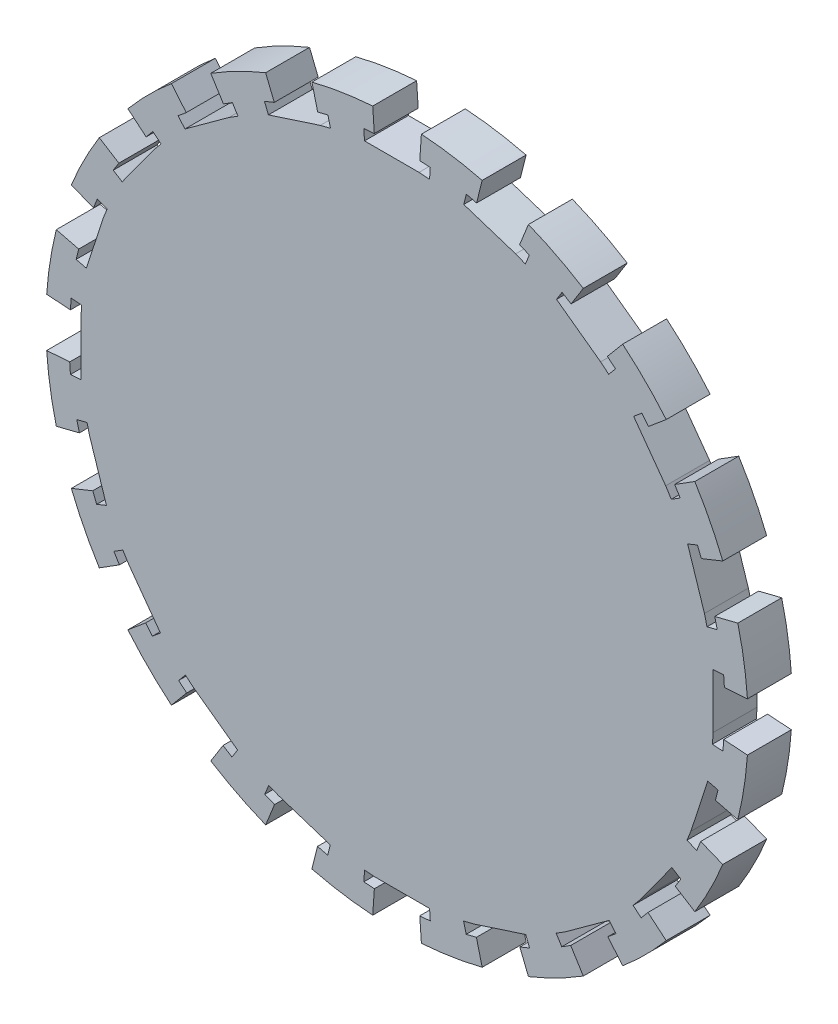
SolidWorks part; units mm, degrees
ref_plane "Front Plane" through (0, 0, 0) normal (0, 0, 1) x (1, 0, 0)
ref_plane "Top Plane" through (0, 0, 0) normal (0, 1, 0) x (1, 0, 0)
ref_plane "Right Plane" through (0, 0, 0) normal (1, 0, 0) x (0, 0, -1)
sketch "Sketch1" plane through (0, 0, 0) normal (0, 0, 1) x (1, 0, 0)
  line L0 (-1.7597, 25.339) -> (-1.5875, 22.86)
  line L1 (-1.5875, 22.86) -> (1.5875, 22.86)
  line L2 (1.5875, 22.86) -> (1.7597, 25.339)
  line L3 (0, 22.86) -> (0, 25.4)
  line L4 (5.5543, 22.2317) -> (8.5739, 21.2506)
  line L5 (8.5739, 21.2506) -> (9.5037, 23.555)
  line L6 (6.1566, 24.6426) -> (5.5543, 22.2317)
  line L7 (12.1525, 19.4272) -> (14.7211, 17.561)
  line L8 (14.7211, 17.561) -> (16.3175, 19.4654)
  line L9 (13.4703, 21.534) -> (12.1525, 19.4272)
  line L10 (17.561, 14.7211) -> (19.4272, 12.1525)
  line L11 (19.4272, 12.1525) -> (21.534, 13.4703)
  line L12 (19.4654, 16.3175) -> (17.561, 14.7211)
  line L13 (21.2506, 8.5739) -> (22.2317, 5.5543)
  line L14 (22.2317, 5.5543) -> (24.6426, 6.1566)
  line L15 (23.555, 9.5037) -> (21.2506, 8.5739)
  line L16 (22.86, 1.5875) -> (22.86, -1.5875)
  line L17 (22.86, -1.5875) -> (25.339, -1.7597)
  line L18 (25.339, 1.7597) -> (22.86, 1.5875)
  line L19 (22.2317, -5.5543) -> (21.2506, -8.5739)
  line L20 (21.2506, -8.5739) -> (23.555, -9.5037)
  line L21 (24.6426, -6.1566) -> (22.2317, -5.5543)
  line L22 (19.4272, -12.1525) -> (17.561, -14.7211)
  line L23 (17.561, -14.7211) -> (19.4654, -16.3175)
  line L24 (21.534, -13.4703) -> (19.4272, -12.1525)
  line L25 (14.7211, -17.561) -> (12.1525, -19.4272)
  line L26 (12.1525, -19.4272) -> (13.4703, -21.534)
  line L27 (16.3175, -19.4654) -> (14.7211, -17.561)
  line L28 (8.5739, -21.2506) -> (5.5543, -22.2317)
  line L29 (5.5543, -22.2317) -> (6.1566, -24.6426)
  line L30 (9.5037, -23.555) -> (8.5739, -21.2506)
  line L31 (1.5875, -22.86) -> (-1.5875, -22.86)
  line L32 (-1.5875, -22.86) -> (-1.7597, -25.339)
  line L33 (1.7597, -25.339) -> (1.5875, -22.86)
  line L34 (-5.5543, -22.2317) -> (-8.5739, -21.2506)
  line L35 (-8.5739, -21.2506) -> (-9.5037, -23.555)
  line L36 (-6.1566, -24.6426) -> (-5.5543, -22.2317)
  line L37 (-12.1525, -19.4272) -> (-14.7211, -17.561)
  line L38 (-14.7211, -17.561) -> (-16.3175, -19.4654)
  line L39 (-13.4703, -21.534) -> (-12.1525, -19.4272)
  line L40 (-17.561, -14.7211) -> (-19.4272, -12.1525)
  line L41 (-19.4272, -12.1525) -> (-21.534, -13.4703)
  line L42 (-19.4654, -16.3175) -> (-17.561, -14.7211)
  line L43 (-21.2506, -8.5739) -> (-22.2317, -5.5543)
  line L44 (-22.2317, -5.5543) -> (-24.6426, -6.1566)
  line L45 (-23.555, -9.5037) -> (-21.2506, -8.5739)
  line L46 (-22.86, -1.5875) -> (-22.86, 1.5875)
  line L47 (-22.86, 1.5875) -> (-25.339, 1.7597)
  line L48 (-25.339, -1.7597) -> (-22.86, -1.5875)
  line L49 (-22.2317, 5.5543) -> (-21.2506, 8.5739)
  line L50 (-21.2506, 8.5739) -> (-23.555, 9.5037)
  line L51 (-24.6426, 6.1566) -> (-22.2317, 5.5543)
  line L52 (-19.4272, 12.1525) -> (-17.561, 14.7211)
  line L53 (-17.561, 14.7211) -> (-19.4654, 16.3175)
  line L54 (-21.534, 13.4703) -> (-19.4272, 12.1525)
  line L55 (-14.7211, 17.561) -> (-12.1525, 19.4272)
  line L56 (-12.1525, 19.4272) -> (-13.4703, 21.534)
  line L57 (-16.3175, 19.4654) -> (-14.7211, 17.561)
  line L58 (-8.5739, 21.2506) -> (-5.5543, 22.2317)
  line L59 (-5.5543, 22.2317) -> (-6.1566, 24.6426)
  line L60 (-9.5037, 23.555) -> (-8.5739, 21.2506)
  line L61 (1.6404, 23.622) -> (2.4024, 23.5691)
  line L62 (2.4024, 23.5691) -> (2.3495, 22.8071)
  line L63 (2.3495, 22.8071) -> (1.5875, 22.86)
  line L64 (-1.644, 23.6731) -> (-2.406, 23.6202)
  line L65 (-2.406, 23.6202) -> (-2.3532, 22.86)
  line L66 (-2.3532, 22.86) -> (-1.5875, 22.86)
  line L67 (5.0108, 23.2076) -> (4.8261, 22.4683)
  line L68 (4.8261, 22.4683) -> (5.5543, 22.2317)
  line L69 (5.7519, 23.0225) -> (5.0108, 23.2076)
  line L70 (8.8597, 21.9589) -> (9.5681, 21.6731)
  line L71 (9.5681, 21.6731) -> (9.2823, 20.9648)
  line L72 (9.2823, 20.9648) -> (8.5739, 21.2506)
  line L73 (11.9371, 20.5233) -> (11.533, 19.8773)
  line L74 (11.533, 19.8773) -> (12.1525, 19.4272)
  line L75 (12.5847, 20.1182) -> (11.9371, 20.5233)
  line L76 (15.2118, 18.1464) -> (15.7972, 17.6557)
  line L77 (15.7972, 17.6557) -> (15.3065, 17.0703)
  line L78 (15.3065, 17.0703) -> (14.7211, 17.561)
  line L79 (17.6949, 15.8301) -> (17.111, 15.3405)
  line L80 (17.111, 15.3405) -> (17.561, 14.7211)
  line L81 (18.1856, 15.2447) -> (17.6949, 15.8301)
  line L82 (20.0748, 12.5575) -> (20.4799, 11.91)
  line L83 (20.4799, 11.91) -> (19.8323, 11.5049)
  line L84 (19.8323, 11.5049) -> (19.4272, 12.1525)
  line L85 (21.7206, 9.5872) -> (21.014, 9.3021)
  line L86 (21.014, 9.3021) -> (21.2506, 8.5739)
  line L87 (22.0064, 8.8789) -> (21.7206, 9.5872)
  line L88 (22.9728, 5.7395) -> (23.1579, 4.9984)
  line L89 (23.1579, 4.9984) -> (22.4169, 4.8133)
  line L90 (22.4169, 4.8133) -> (22.2317, 5.5543)
  line L91 (23.6202, 2.406) -> (22.86, 2.3532)
  line L92 (22.86, 2.3532) -> (22.86, 1.5875)
  line L93 (23.6731, 1.644) -> (23.6202, 2.406)
  line L94 (23.622, -1.6404) -> (23.5691, -2.4024)
  line L95 (23.5691, -2.4024) -> (22.8071, -2.3495)
  line L96 (22.8071, -2.3495) -> (22.86, -1.5875)
  line L97 (23.2076, -5.0108) -> (22.4683, -4.8261)
  line L98 (22.4683, -4.8261) -> (22.2317, -5.5543)
  line L99 (23.0225, -5.7519) -> (23.2076, -5.0108)
  line L100 (21.9589, -8.8597) -> (21.6731, -9.5681)
  line L101 (21.6731, -9.5681) -> (20.9648, -9.2823)
  line L102 (20.9648, -9.2823) -> (21.2506, -8.5739)
  line L103 (20.5233, -11.9371) -> (19.8773, -11.533)
  line L104 (19.8773, -11.533) -> (19.4272, -12.1525)
  line L105 (20.1182, -12.5847) -> (20.5233, -11.9371)
  line L106 (18.1464, -15.2118) -> (17.6557, -15.7972)
  line L107 (17.6557, -15.7972) -> (17.0703, -15.3065)
  line L108 (17.0703, -15.3065) -> (17.561, -14.7211)
  line L109 (15.8301, -17.6949) -> (15.3405, -17.111)
  line L110 (15.3405, -17.111) -> (14.7211, -17.561)
  line L111 (15.2447, -18.1856) -> (15.8301, -17.6949)
  line L112 (12.5575, -20.0748) -> (11.91, -20.4799)
  line L113 (11.91, -20.4799) -> (11.5049, -19.8323)
  line L114 (11.5049, -19.8323) -> (12.1525, -19.4272)
  line L115 (9.5872, -21.7206) -> (9.3021, -21.014)
  line L116 (9.3021, -21.014) -> (8.5739, -21.2506)
  line L117 (8.8789, -22.0064) -> (9.5872, -21.7206)
  line L118 (5.7395, -22.9728) -> (4.9984, -23.1579)
  line L119 (4.9984, -23.1579) -> (4.8133, -22.4169)
  line L120 (4.8133, -22.4169) -> (5.5543, -22.2317)
  line L121 (2.406, -23.6202) -> (2.3532, -22.86)
  line L122 (2.3532, -22.86) -> (1.5875, -22.86)
  line L123 (1.644, -23.6731) -> (2.406, -23.6202)
  line L124 (-1.6404, -23.622) -> (-2.4024, -23.5691)
  line L125 (-2.4024, -23.5691) -> (-2.3495, -22.8071)
  line L126 (-2.3495, -22.8071) -> (-1.5875, -22.86)
  line L127 (-5.0108, -23.2076) -> (-4.8261, -22.4683)
  line L128 (-4.8261, -22.4683) -> (-5.5543, -22.2317)
  line L129 (-5.7519, -23.0225) -> (-5.0108, -23.2076)
  line L130 (-8.8597, -21.9589) -> (-9.5681, -21.6731)
  line L131 (-9.5681, -21.6731) -> (-9.2823, -20.9648)
  line L132 (-9.2823, -20.9648) -> (-8.5739, -21.2506)
  line L133 (-11.9371, -20.5233) -> (-11.533, -19.8773)
  line L134 (-11.533, -19.8773) -> (-12.1525, -19.4272)
  line L135 (-12.5847, -20.1182) -> (-11.9371, -20.5233)
  line L136 (-15.2118, -18.1464) -> (-15.7972, -17.6557)
  line L137 (-15.7972, -17.6557) -> (-15.3065, -17.0703)
  line L138 (-15.3065, -17.0703) -> (-14.7211, -17.561)
  line L139 (-17.6949, -15.8301) -> (-17.111, -15.3405)
  line L140 (-17.111, -15.3405) -> (-17.561, -14.7211)
  line L141 (-18.1856, -15.2447) -> (-17.6949, -15.8301)
  line L142 (-20.0748, -12.5575) -> (-20.4799, -11.91)
  line L143 (-20.4799, -11.91) -> (-19.8323, -11.5049)
  line L144 (-19.8323, -11.5049) -> (-19.4272, -12.1525)
  line L145 (-21.7206, -9.5872) -> (-21.014, -9.3021)
  line L146 (-21.014, -9.3021) -> (-21.2506, -8.5739)
  line L147 (-22.0064, -8.8789) -> (-21.7206, -9.5872)
  line L148 (-22.9728, -5.7395) -> (-23.1579, -4.9984)
  line L149 (-23.1579, -4.9984) -> (-22.4169, -4.8133)
  line L150 (-22.4169, -4.8133) -> (-22.2317, -5.5543)
  line L151 (-23.6202, -2.406) -> (-22.86, -2.3532)
  line L152 (-22.86, -2.3532) -> (-22.86, -1.5875)
  line L153 (-23.6731, -1.644) -> (-23.6202, -2.406)
  line L154 (-23.622, 1.6404) -> (-23.5691, 2.4024)
  line L155 (-23.5691, 2.4024) -> (-22.8071, 2.3495)
  line L156 (-22.8071, 2.3495) -> (-22.86, 1.5875)
  line L157 (-23.2076, 5.0108) -> (-22.4683, 4.8261)
  line L158 (-22.4683, 4.8261) -> (-22.2317, 5.5543)
  line L159 (-23.0225, 5.7519) -> (-23.2076, 5.0108)
  line L160 (-21.9589, 8.8597) -> (-21.6731, 9.5681)
  line L161 (-21.6731, 9.5681) -> (-20.9648, 9.2823)
  line L162 (-20.9648, 9.2823) -> (-21.2506, 8.5739)
  line L163 (-20.5233, 11.9371) -> (-19.8773, 11.533)
  line L164 (-19.8773, 11.533) -> (-19.4272, 12.1525)
  line L165 (-20.1182, 12.5847) -> (-20.5233, 11.9371)
  line L166 (-18.1464, 15.2118) -> (-17.6557, 15.7972)
  line L167 (-17.6557, 15.7972) -> (-17.0703, 15.3065)
  line L168 (-17.0703, 15.3065) -> (-17.561, 14.7211)
  line L169 (-15.8301, 17.6949) -> (-15.3405, 17.111)
  line L170 (-15.3405, 17.111) -> (-14.7211, 17.561)
  line L171 (-15.2447, 18.1856) -> (-15.8301, 17.6949)
  line L172 (-12.5575, 20.0748) -> (-11.91, 20.4799)
  line L173 (-11.91, 20.4799) -> (-11.5049, 19.8323)
  line L174 (-11.5049, 19.8323) -> (-12.1525, 19.4272)
  line L175 (-9.5872, 21.7206) -> (-9.3021, 21.014)
  line L176 (-9.3021, 21.014) -> (-8.5739, 21.2506)
  line L177 (-8.8789, 22.0064) -> (-9.5872, 21.7206)
  line L178 (-5.7395, 22.9728) -> (-4.9984, 23.1579)
  line L179 (-4.9984, 23.1579) -> (-4.8133, 22.4169)
  line L180 (-4.8133, 22.4169) -> (-5.5543, 22.2317)
  arc A0 (-9.5037, 23.555) -> (-13.4703, 21.534) centre (0, 0) ccw
  arc A1 (-16.3175, 19.4654) -> (-19.4654, 16.3175) centre (0, 0) ccw
  arc A2 (-21.534, 13.4703) -> (-23.555, 9.5037) centre (0, 0) ccw
  arc A3 (-24.6426, 6.1566) -> (-25.339, 1.7597) centre (0, 0) ccw
  arc A4 (-25.339, -1.7597) -> (-24.6426, -6.1566) centre (0, 0) ccw
  arc A5 (-23.555, -9.5037) -> (-21.534, -13.4703) centre (0, 0) ccw
  arc A6 (-1.7597, 25.339) -> (-6.1566, 24.6426) centre (0, 0) ccw
  arc A7 (6.1566, 24.6426) -> (1.7597, 25.339) centre (0, 0) ccw
  arc A8 (13.4703, 21.534) -> (9.5037, 23.555) centre (0, 0) ccw
  arc A9 (19.4654, 16.3175) -> (16.3175, 19.4654) centre (0, 0) ccw
  arc A10 (23.555, 9.5037) -> (21.534, 13.4703) centre (0, 0) ccw
  arc A11 (25.339, 1.7597) -> (24.6426, 6.1566) centre (0, 0) ccw
  arc A12 (24.6426, -6.1566) -> (25.339, -1.7597) centre (0, 0) ccw
  arc A13 (21.534, -13.4703) -> (23.555, -9.5037) centre (0, 0) ccw
  arc A14 (16.3175, -19.4654) -> (19.4654, -16.3175) centre (0, 0) ccw
  arc A15 (9.5037, -23.555) -> (13.4703, -21.534) centre (0, 0) ccw
  arc A16 (1.7597, -25.339) -> (6.1566, -24.6426) centre (0, 0) ccw
  arc A17 (-6.1566, -24.6426) -> (-1.7597, -25.339) centre (0, 0) ccw
  arc A18 (-13.4703, -21.534) -> (-9.5037, -23.555) centre (0, 0) ccw
  arc A19 (-19.4654, -16.3175) -> (-16.3175, -19.4654) centre (0, 0) ccw
  point P88 (0, 0)
  point P246 (0, 0)
  dimension "D1" = 50.8
  dimension "D2" = 2.54
  dimension "D3" = 3.175
  dimension "D5" = 0.762
  dimension "D6" = 0.762
  dimension "D7" = 0.762
  dimension "D8" = 0.762
  dimension "D4" = 20
  dimension "D9" = 20
extrude "Boss-Extrude1" add sketch "Sketch1" along normal blind 3.175 contours L42 A19 L38 L37 L39 A18 L35 L34 L36 A17 L32 L31 L33 A16 L29 L28 L30 A15 L26 L25 L27 A14 L23 L22 L24 A13 L20 L19 L21 A12 L17 L16 L18 A11 L14 L13 L15 A10 L11 L10 L12 A9 L8 L7 L9 A8 L5 L4 L6 A7 L2
